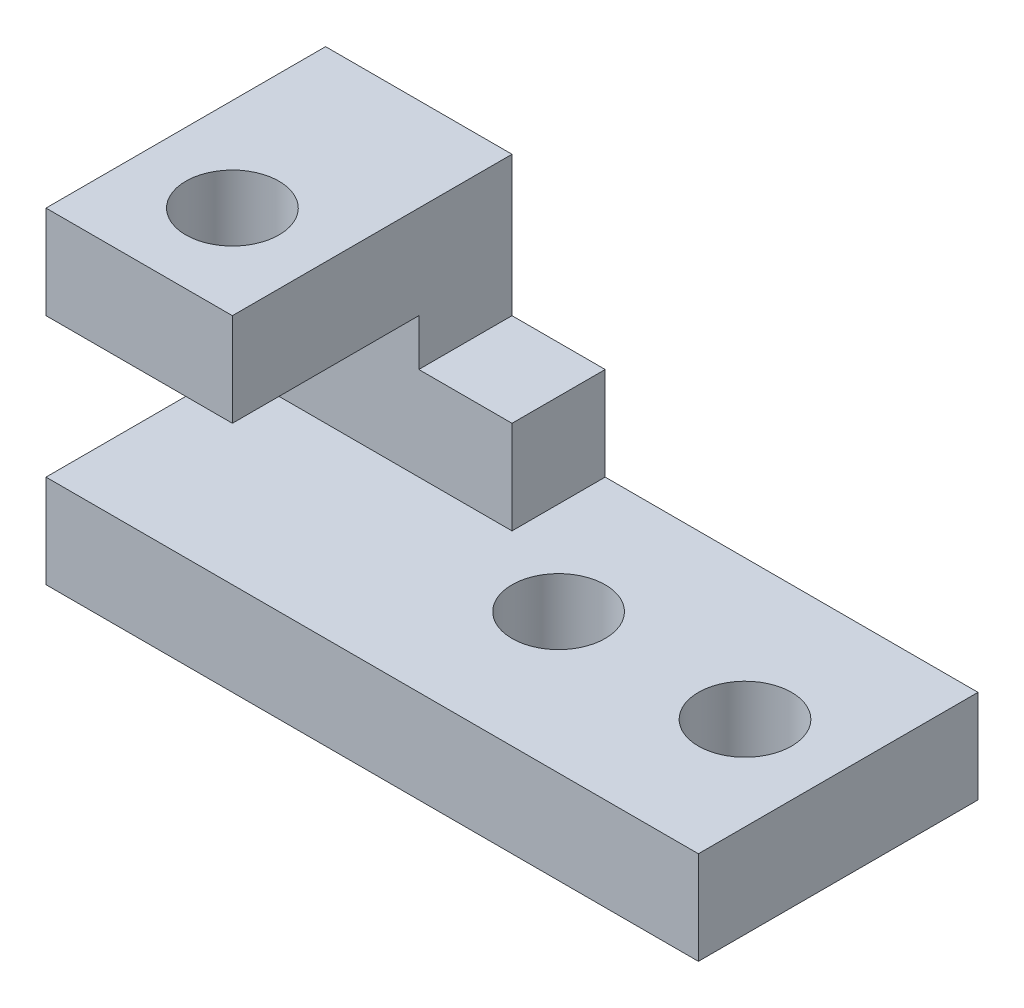
SolidWorks part; units mm, degrees
ref_plane "Front Plane" through (0, 0, 0) normal (0, 0, 1) x (1, 0, 0)
ref_plane "Top Plane" through (0, 0, 0) normal (0, 1, 0) x (1, 0, 0)
ref_plane "Right Plane" through (0, 0, 0) normal (1, 0, 0) x (0, 0, -1)
sketch "Sketch1" plane through (0, 0, 0) normal (0, 1, 0) x (1, 0, 0)
  line L1 (0, 0) -> (70, 0)
  line L2 (0, 0) -> (0, 30)
  line L3 (0, 30) -> (70, 30)
  line L4 (70, 0) -> (70, 30)
  dimension "D1" = 70
  dimension "D2" = 30
extrude "Boss-Extrude2" add sketch "Sketch1" along normal blind 10
sketch "Sketch3" plane through (0, 10, 0) normal (0, 1, 0) x (1, 0, 0)
  line L1 (0, 30) -> (30, 30)
  line L2 (0, 30) -> (0, 20)
  line L3 (0, 20) -> (30, 20)
  line L4 (30, 30) -> (30, 20)
  dimension "D1" = 10
  dimension "D2" = 30
extrude "Boss-Extrude3" add sketch "Sketch3" along normal blind 25
sketch "Sketch4" plane through (0, 0, -20) normal (0, 0, 1) x (1, 0, 0)
  line L1 (30, 35) -> (20, 35)
  line L2 (30, 35) -> (30, 20)
  line L3 (30, 20) -> (20, 20)
  line L4 (20, 35) -> (20, 20)
  dimension "D1" = 10
  dimension "D2" = 15
extrude "Cut-Extrude1" cut sketch "Sketch4" against normal through all
sketch "Sketch5" plane through (0, 0, -20) normal (0, 0, 1) x (1, 0, 0)
  line L0 (20, 35) -> (20, 20) construction
  line L1 (0, 35) -> (20, 35)
  line L2 (0, 35) -> (0, 25)
  line L3 (0, 25) -> (20, 25)
  line L4 (20, 35) -> (20, 25)
  dimension "D1" = 10
extrude "Boss-Extrude4" add sketch "Sketch5" along normal blind 20
sketch "Sketch6" plane through (0, 10, 0) normal (0, 1, 0) x (1, 0, 0)
  line L0 (30, 20) -> (40, 20) construction
  line L1 (40, 20) -> (40, 15) construction
  line L2 (40, 15) -> (60, 15) construction
  circle A0 centre (40, 15) radius 5
  circle A1 centre (60, 15) radius 5
  dimension "D1" = 10
  dimension "D2" = 5
  dimension "D3" = 20
extrude "Cut-Extrude2" cut sketch "Sketch6" against normal through all
sketch "Sketch7" plane through (0, 35, 0) normal (0, 1, 0) x (1, 0, 0)
  line L0 (0, 0) -> (0, 10) construction
  line L1 (0, 30) -> (0, 0) construction
  line L2 (0, 10) -> (10, 10) construction
  circle A0 centre (10, 10) radius 5
  dimension "D2" = 10
  dimension "D1" = 10
extrude "Cut-Extrude3" cut sketch "Sketch7" against normal blind 15
